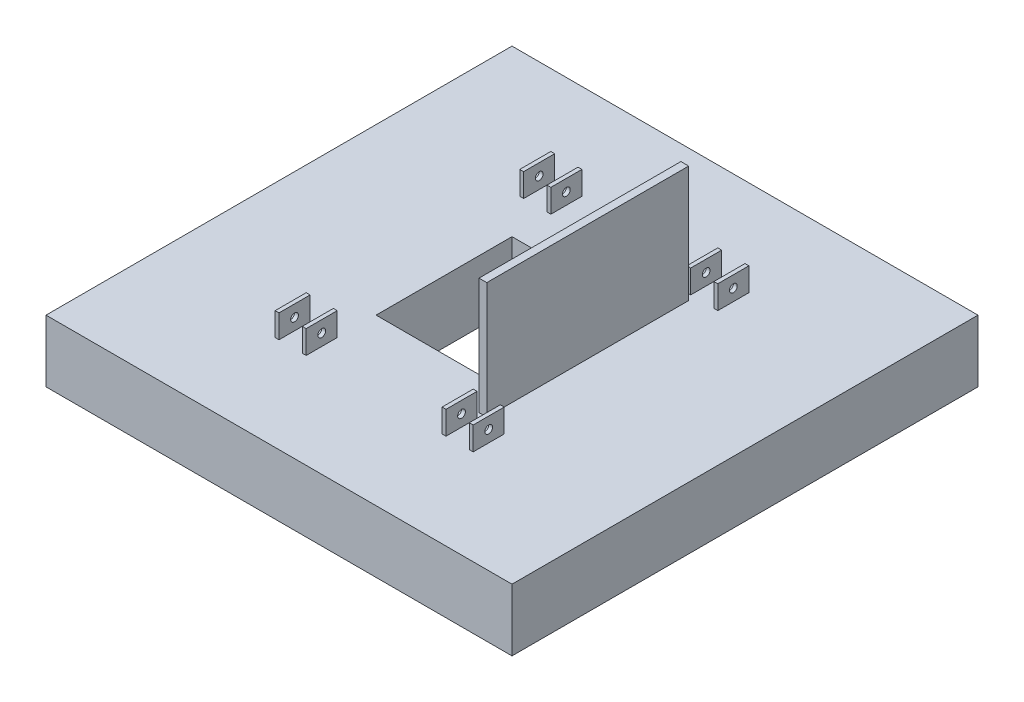
SolidWorks part; units mm, degrees
ref_plane "Front Plane" through (0, 0, 0) normal (0, 0, 1) x (1, 0, 0)
ref_plane "Top Plane" through (0, 0, 0) normal (0, 1, 0) x (1, 0, 0)
ref_plane "Right Plane" through (0, 0, 0) normal (1, 0, 0) x (0, 0, -1)
sketch "Sketch1" plane through (0, 0, 0) normal (0, 1, 0) x (1, 0, 0)
  line L0 (-381, -381) -> (381, -381)
  line L1 (-381, -381) -> (-381, 381)
  line L2 (-381, 381) -> (381, 381)
  line L3 (381, -381) -> (381, 381)
  line L4 (-381, -381) -> (381, 381) construction
  line L5 (-381, 381) -> (381, -381) construction
  point P0 (0, 0)
  dimension "D1" = 762
extrude "Boss-Extrude1" add sketch "Sketch1" along normal blind 101.6
sketch "Sketch2" plane through (0, 101.6, 0) normal (0, 1, 0) x (1, 0, 0)
  line L1 (-111.125, -111.125) -> (111.125, -111.125)
  line L2 (-111.125, -111.125) -> (-111.125, 111.125)
  line L3 (-111.125, 111.125) -> (111.125, 111.125)
  line L4 (111.125, -111.125) -> (111.125, 111.125)
  line L5 (-111.125, -111.125) -> (111.125, 111.125) construction
  line L6 (-111.125, 111.125) -> (111.125, -111.125) construction
  point P0 (0, 0)
  dimension "D1" = 222.25
extrude "Cut-Extrude1" cut sketch "Sketch2" against normal through all contours L2 L1 L4 L3
sketch "Sketch3" plane through (0, 101.6, 0) normal (0, 1, 0) x (1, 0, 0)
  line L0 (111.125, 165.1) -> (123.825, 165.1)
  line L1 (111.125, 165.1) -> (111.125, -165.1)
  line L2 (111.125, -165.1) -> (123.825, -165.1)
  line L3 (123.825, 165.1) -> (123.825, -165.1)
  line L5 (111.125, -111.125) -> (111.125, 111.125) construction
  point P4 (111.125, 0)
  point P7 (111.125, 0)
  dimension "D1" = 330.2
  dimension "D2" = 12.7
extrude "Boss-Extrude2" add sketch "Sketch3" along normal blind 190.5
sketch "Sketch4" plane through (0, 101.6, 0) normal (0, 1, 0) x (1, 0, 0)
  line L9 (-161.925, -174.625) -> (-155.575, -174.625)
  line L10 (-161.925, -174.625) -> (-161.925, -225.425)
  line L11 (-161.925, -225.425) -> (-155.575, -225.425)
  line L12 (-111.125, -174.625) -> (-111.125, -225.425)
  line L17 (-111.125, -111.125) -> (111.125, -111.125) construction
  line L28 (-155.575, -174.625) -> (-155.575, -225.425)
  line L29 (-117.475, -174.625) -> (-117.475, -225.425)
  line L30 (-155.575, -200.025) -> (-161.925, -200.025) construction
  line L31 (-117.475, -200.025) -> (-111.125, -200.025) construction
  line L32 (-117.475, -174.625) -> (-111.125, -174.625)
  line L33 (-117.475, -225.425) -> (-111.125, -225.425)
  line L34 (0, -160.655) -> (0, 160.655) construction
  line L35 (117.475, -200.025) -> (111.125, -200.025) construction
  line L36 (155.575, -200.025) -> (161.925, -200.025) construction
  line L37 (117.475, -225.425) -> (111.125, -225.425)
  line L38 (117.475, -174.625) -> (111.125, -174.625)
  line L39 (117.475, -174.625) -> (117.475, -225.425)
  line L40 (155.575, -174.625) -> (155.575, -225.425)
  line L41 (111.125, -174.625) -> (111.125, -225.425)
  line L42 (161.925, -225.425) -> (155.575, -225.425)
  line L43 (161.925, -174.625) -> (161.925, -225.425)
  line L44 (161.925, -174.625) -> (155.575, -174.625)
  line L45 (-160.655, 0) -> (160.655, 0) construction
  line L46 (155.575, 200.025) -> (161.925, 200.025) construction
  line L47 (117.475, 200.025) -> (111.125, 200.025) construction
  line L48 (-117.475, 200.025) -> (-111.125, 200.025) construction
  line L49 (-155.575, 200.025) -> (-161.925, 200.025) construction
  line L50 (161.925, 174.625) -> (155.575, 174.625)
  line L51 (161.925, 174.625) -> (161.925, 225.425)
  line L52 (161.925, 225.425) -> (155.575, 225.425)
  line L53 (111.125, 174.625) -> (111.125, 225.425)
  line L54 (155.575, 174.625) -> (155.575, 225.425)
  line L55 (117.475, 174.625) -> (117.475, 225.425)
  line L56 (117.475, 174.625) -> (111.125, 174.625)
  line L57 (117.475, 225.425) -> (111.125, 225.425)
  line L58 (-117.475, 225.425) -> (-111.125, 225.425)
  line L59 (-117.475, 174.625) -> (-111.125, 174.625)
  line L60 (-117.475, 174.625) -> (-117.475, 225.425)
  line L61 (-155.575, 174.625) -> (-155.575, 225.425)
  line L62 (-111.125, 174.625) -> (-111.125, 225.425)
  line L63 (-161.925, 225.425) -> (-155.575, 225.425)
  line L64 (-161.925, 174.625) -> (-161.925, 225.425)
  line L65 (-161.925, 174.625) -> (-155.575, 174.625)
  line L66 (-111.125, -111.125) -> (-111.125, 111.125) construction
  dimension "D1" = 50.8
  dimension "D2" = 63.5
  dimension "D3" = 6.35
  dimension "D4" = 50.8
extrude "Boss-Extrude3" add sketch "Sketch4" along normal blind 38.1
sketch "Sketch6" plane through (-161.925, 0, 0) normal (-1, 0, 0) x (0, 0, 1)
  line L0 (-225.425, 139.7) -> (-225.425, 101.6) construction
  line L1 (-225.425, 139.7) -> (-174.625, 139.7) construction
  line L2 (174.625, 139.7) -> (174.625, 101.6) construction
  line L3 (174.625, 139.7) -> (225.425, 139.7) construction
  circle A0 centre (-200.025, 120.65) radius 6.35
  circle A1 centre (200.025, 120.65) radius 6.35
  point P7 (-225.425, 120.65)
  point P10 (-200.025, 139.7)
  point P14 (174.625, 120.65)
  point P17 (200.025, 139.7)
  dimension "D1" = 12.7
extrude "Cut-Extrude2" cut sketch "Sketch6" against normal through all
